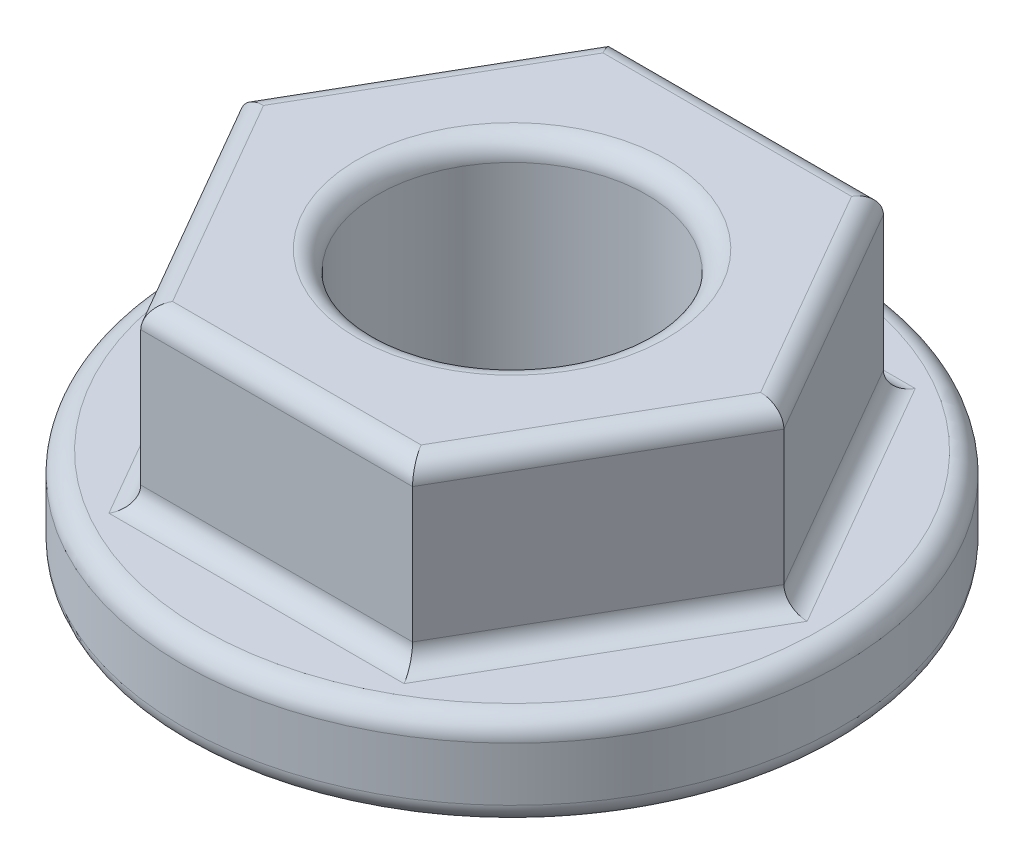
SolidWorks part; units mm, degrees
ref_plane "Front Plane" through (0, 0, 0) normal (0, 0, 1) x (1, 0, 0)
ref_plane "Top Plane" through (0, 0, 0) normal (0, 1, 0) x (1, 0, 0)
ref_plane "Right Plane" through (0, 0, 0) normal (1, 0, 0) x (0, 0, -1)
sketch "Sketch1" plane through (0, 0, 0) normal (0, 1, 0) x (1, 0, 0)
  circle A0 centre (0, 0) radius 4.9
  dimension "D1" = 9.8
extrude "Boss-Extrude1" add sketch "Sketch1" along normal blind 4
sketch "Sketch2" plane through (0, 4, 0) normal (0, 1, 0) x (1, 0, 0)
  circle A0 centre (0, 0) radius 2
  dimension "D1" = 4
extrude "Cut-Extrude1" cut sketch "Sketch2" against normal blind 4.8
sketch "Sketch3" plane through (0, 4, 0) normal (0, 1, 0) x (1, 0, 0)
  line L1 (4.0415, 0) -> (2.0207, 3.5)
  line L2 (2.0207, 3.5) -> (-2.0207, 3.5)
  line L3 (-2.0207, 3.5) -> (-4.0415, 0)
  line L4 (-4.0415, 0) -> (-2.0207, -3.5)
  line L5 (-2.0207, -3.5) -> (2.0207, -3.5)
  line L6 (2.0207, -3.5) -> (4.0415, 0)
  circle A0 centre (0, 0) radius 3.5 construction
  dimension "D1" = 7
extrude "Cut-Extrude2" cut sketch "Sketch3" against normal blind 2.6 flip side to cut
fillet "Fillet1" radius 0.3 16 edges at (0, 0, 4.9) (0, 0, 2) (0, 1.4, 4.9) (3.0311, 1.4, 1.75) (3.0311, 1.4, -1.75) (0, 1.4, -3.5) (-3.0311, 1.4, -1.75) (-3.0311, 1.4, 1.75) (0, 1.4, 3.5) (-3.0311, 4, 1.75) (-3.0311, 4, -1.75) (0, 4, -3.5) (3.0311, 4, -1.75) (3.0311, 4, 1.75) (0, 4, 3.5) (0, 4, 2)
